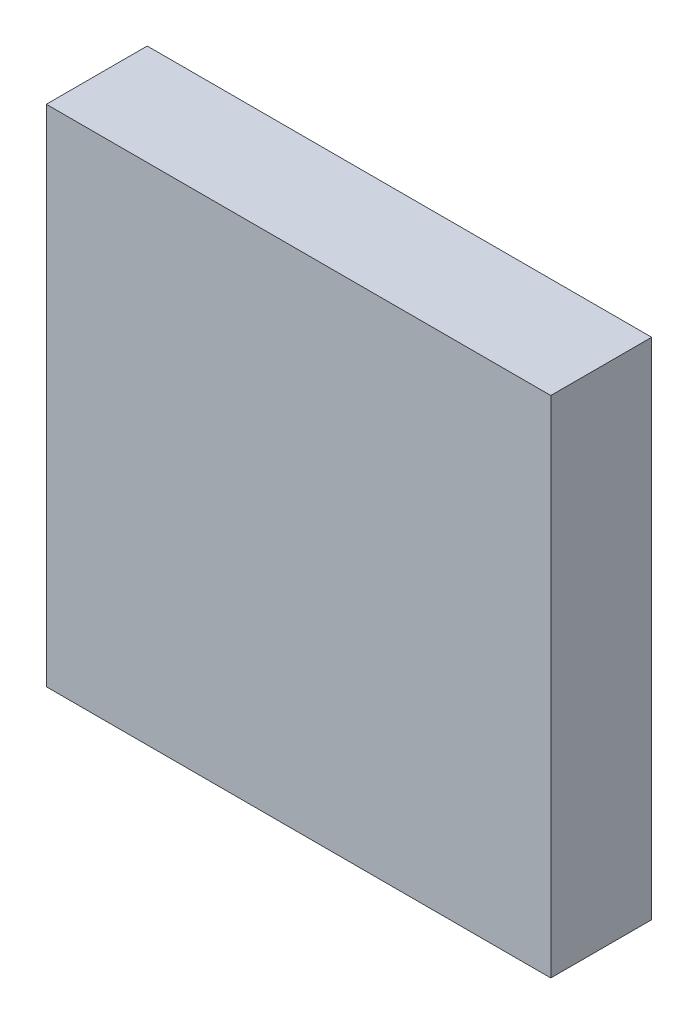
SolidWorks part; units mm, degrees
ref_plane "Plan de face" through (0, 0, 0) normal (0, 0, 1) x (1, 0, 0)
ref_plane "Plan de dessus" through (0, 0, 0) normal (0, 1, 0) x (1, 0, 0)
ref_plane "Plan de droite" through (0, 0, 0) normal (1, 0, 0) x (0, 0, -1)
sketch "Esquisse1" plane through (0, 0, 0) normal (0, 0, 1) x (1, 0, 0)
  line L1 (-2, -2) -> (2, -2)
  line L2 (-2, -2) -> (-2, 2)
  line L3 (-2, 2) -> (2, 2)
  line L4 (2, -2) -> (2, 2)
  line L5 (-2, -2) -> (2, 2) construction
  line L6 (-2, 2) -> (2, -2) construction
  point P0 (0, 0)
  dimension "D1" = 4
  dimension "D2" = 4
extrude "Boss.-Extru.1" add sketch "Esquisse1" along normal blind 0.8
